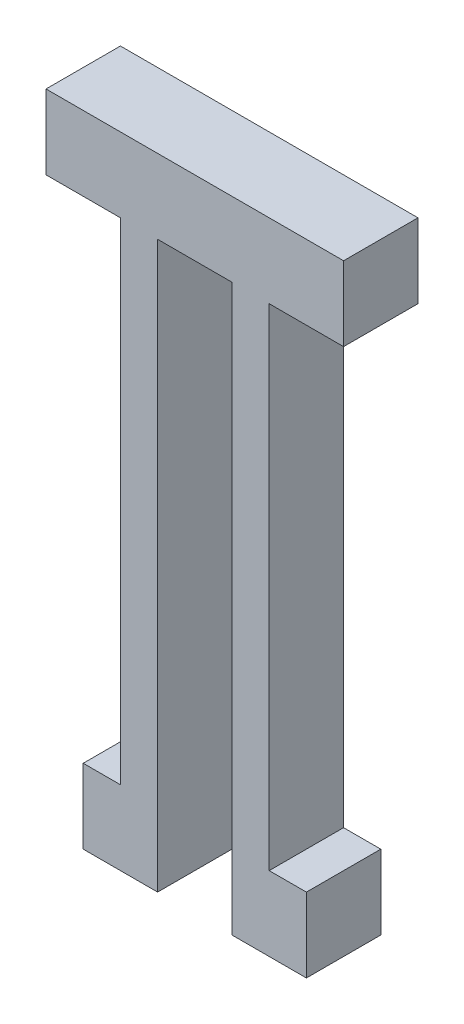
SolidWorks part; units mm, degrees
ref_plane "Front Plane" through (0, 0, 0) normal (0, 0, 1) x (1, 0, 0)
ref_plane "Top Plane" through (0, 0, 0) normal (0, 1, 0) x (1, 0, 0)
ref_plane "Right Plane" through (0, 0, 0) normal (1, 0, 0) x (0, 0, -1)
sketch "Sketch1" plane through (0, 0, 0) normal (0, 0, 1) x (1, 0, 0)
  line L0 (9.525, -48.26) -> (15.875, -48.26) construction
  line L1 (0, 0) -> (6.35, 0)
  line L2 (0, 0) -> (0, 6.35)
  line L3 (0, 6.35) -> (25.4, 6.35)
  line L4 (25.4, 0) -> (25.4, 6.35)
  line L5 (19.05, 0) -> (25.4, 0)
  line L6 (6.35, 0) -> (6.35, -41.91)
  line L7 (6.35, -48.26) -> (9.525, -48.26)
  line L8 (9.525, 0) -> (9.525, -48.26)
  line L10 (15.875, 0) -> (15.875, -48.26)
  line L11 (15.875, -48.26) -> (19.05, -48.26)
  line L12 (19.05, 0) -> (19.05, -41.91)
  line L13 (19.05, -41.91) -> (22.225, -41.91)
  line L15 (19.05, -48.26) -> (22.225, -48.26)
  line L16 (22.225, -41.91) -> (22.225, -48.26)
  line L17 (6.35, -41.91) -> (3.175, -41.91)
  line L19 (6.35, -48.26) -> (3.175, -48.26)
  line L20 (3.175, -41.91) -> (3.175, -48.26)
  line L21 (9.525, 0) -> (15.875, 0)
  dimension "D1" = 6.35
  dimension "D2" = 25.4
  dimension "D3" = 19.05
  dimension "D4" = 6.35
  dimension "D5" = 3.175
  dimension "D6" = 3.175
  dimension "D7" = 41.91
extrude "Boss-Extrude1" add sketch "Sketch1" along normal blind 6.35
ref_plane "Plane1" through (12.7, 0, 0) normal (-1, 0, 0) x (0, 0, 1)
